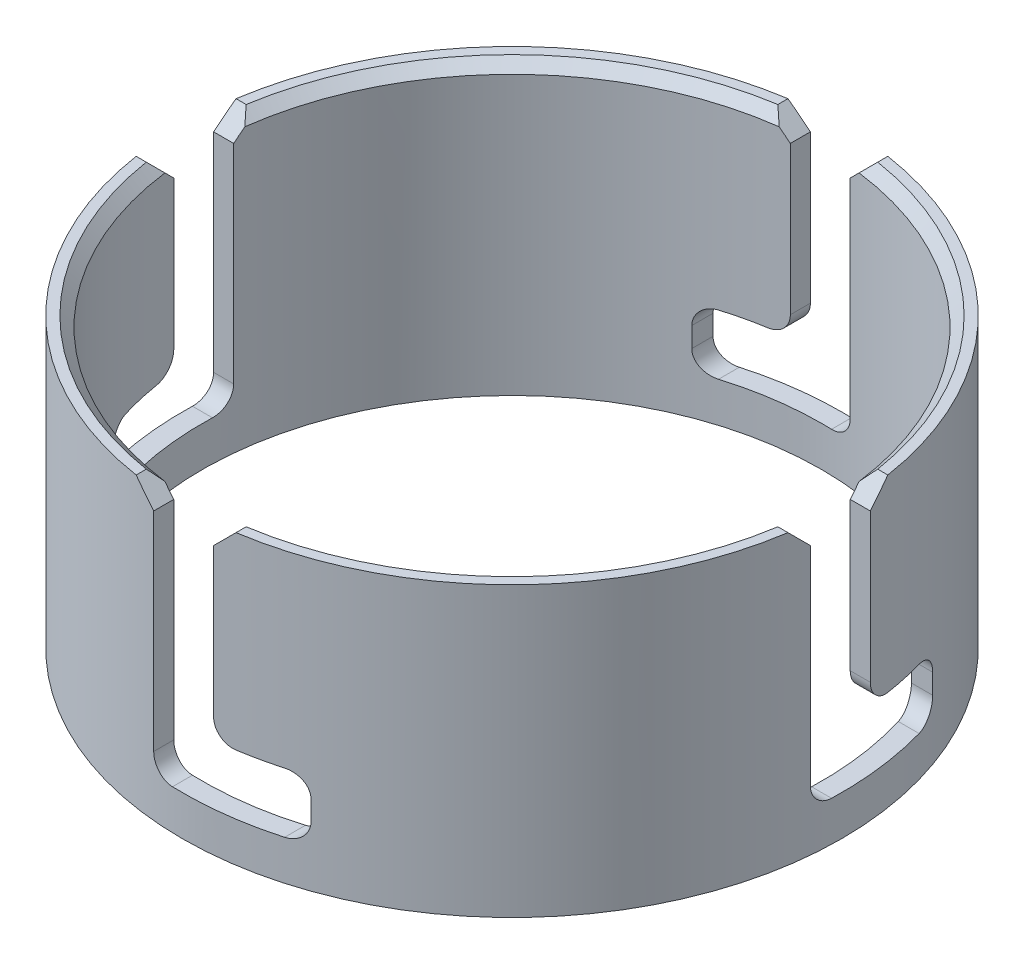
SolidWorks part; units mm, degrees
material "Plain Carbon Steel"
ref_plane "Front Plane" through (0, 0, 0) normal (0, 0, 1) x (1, 0, 0)
ref_plane "Top Plane" through (0, 0, 0) normal (0, 1, 0) x (1, 0, 0)
ref_plane "Right Plane" through (0, 0, 0) normal (1, 0, 0) x (0, 0, -1)
sketch "Sketch2" plane through (0, 0, 0) normal (1, 0, 0) x (0, 0, -1)
  line L0 (-77.55, 0) -> (-82.55, 0)
  line L1 (-82.55, 0) -> (-82.55, 72.15)
  line L2 (-82.55, 72.15) -> (-77.55, 72.15)
  line L5 (-77.55, 72.15) -> (-77.55, 0)
  dimension "D1" = 82.55
  dimension "D2" = 72.15
  dimension "D3" = 5
ref_axis "Axis1" through (0, -3.6075, 0) along (0, 1, 0)
revolve "Revolve1" add sketch "Sketch2" angle 360 about axis through (0, -3.6075, 0) along (0, 1, 0)
sketch "Sketch3" plane through (0, 0, 0) normal (1, 0, 0) x (0, 0, -1)
  line L0 (-7.5, 72.15) -> (7.5, 72.15)
  line L1 (82.55, 72.15) -> (-82.55, 72.15) construction
  line L2 (7.5, 72.15) -> (7.5, 10)
  line L3 (7.5, 10) -> (-27.5, 10)
  line L4 (-27.5, 10) -> (-27.5, 25)
  line L5 (-27.5, 25) -> (-7.5, 25)
  line L6 (-7.5, 25) -> (-7.5, 72.15)
  line L7 (0, -3.6075) -> (0, 75.7575) construction
  line L8 (0, 0) -> (0, 47.5309) construction
  line L9 (-82.55, 0) -> (82.55, 0) construction
  dimension "D1" = 10
  dimension "D2" = 15
  dimension "D3" = 15
  dimension "D4" = 20
extrude "Cut-Extrude1" cut sketch "Sketch3" against normal through all
fillet "Fillet1" radius 5 2 edges at (-79.6975, 25, 7.5) (-79.6975, 10, -7.5)
chamfer "Chamfer1" distance 5 angle 45 2 edges at (-79.6975, 72.15, 7.5) (-79.6975, 72.15, -7.5)
fillet "Fillet3" radius 5 2 edges at (-75.1726, 25, 27.5) (-75.1726, 10, 27.5)
pattern_circular "CirPattern1" count 4 over 360 about axis through (0, 0, 0) along (0, 1, 0) of "Fillet3", "Chamfer1", "Fillet1", "Cut-Extrude1"
chamfer "Chamfer2" distance 2.5 angle 45 4 edges at (-54.8361, 72.15, -54.8361) (54.8361, 72.15, -54.8361) (54.8361, 72.15, 54.8361) (-54.8361, 72.15, 54.8361)
equation "\"TubeDiameter\" = 6.500in"
equation "\"D1@Sketch2\"=\"TubeDiameter\"/2"
